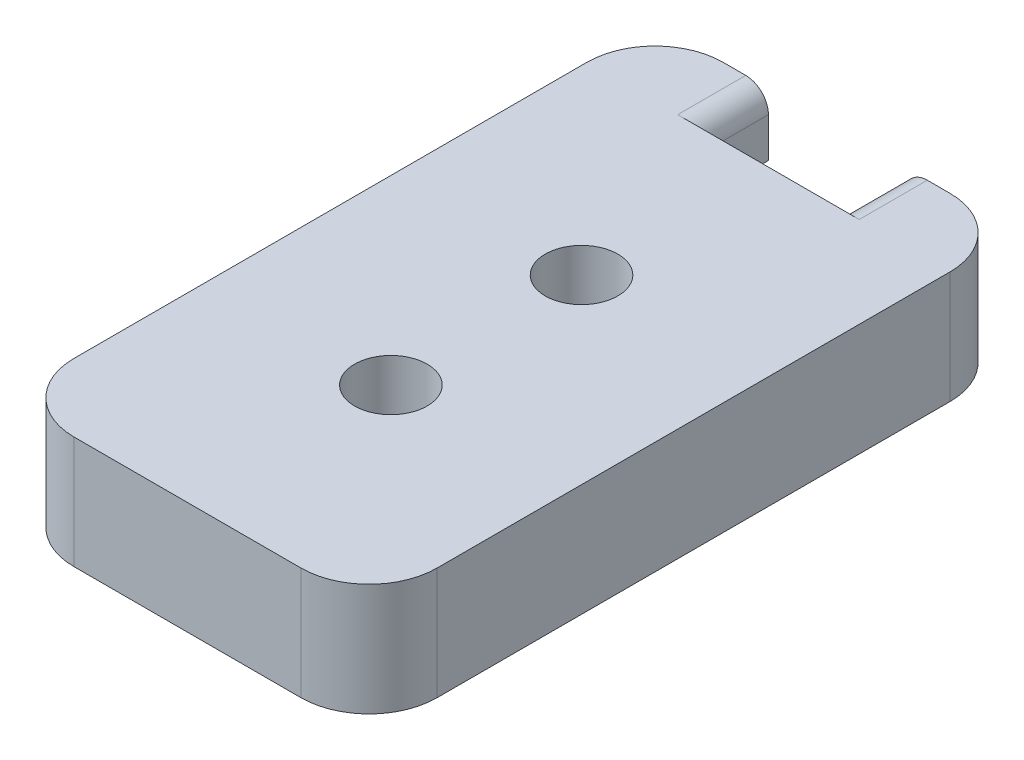
SolidWorks part; units mm, degrees
ref_plane "前视基准面" through (0, 0, 0) normal (0, 0, 1) x (1, 0, 0)
ref_plane "上视基准面" through (0, 0, 0) normal (0, 1, 0) x (1, 0, 0)
ref_plane "右视基准面" through (0, 0, 0) normal (1, 0, 0) x (0, 0, -1)
sketch "草图2" plane through (0, 0, 0) normal (0, 0, 1) x (1, 0, 0)
  line L0 (0, 0) -> (20, 0)
  line L1 (20, 0) -> (20, -4.95)
  line L2 (20, -4.95) -> (0, -4.95)
  line L3 (0, -4.95) -> (0, 0)
  point P2 (0, 0)
  point P5 (0, 0)
  point P6 (0, 0)
  point P7 (0, 0)
  point P8 (0, 0)
  point P9 (0.8017, 0)
extrude "凸台-拉伸1" add sketch "草图2" along normal blind 25.6
sketch "草图3" plane through (0, 0, 0) normal (0, 1, 0) x (1, 0, 0)
  circle A0 centre (10, -8.2367) radius 1.6
  circle A1 centre (10, -16.6367) radius 1.6
  dimension "D1" = 3.2
  dimension "D2" = 3.2
extrude "切除-拉伸1" cut sketch "草图3" against normal through all
sketch "草图4" plane through (0, 0, 0) normal (0, 0, -1) x (-1, 0, 0)
  line L0 (0, -4.95) -> (0, 0)
  line L1 (0, 0) -> (-20, 0)
  line L2 (-20, 0) -> (-20, -4.95)
  line L3 (-20, -4.95) -> (0, -4.95)
extrude "凸台-拉伸2" add sketch "草图4" along normal blind 3
sketch "草图5" plane through (0, 0, -3) normal (0, 0, -1) x (-1, 0, 0)
  line L0 (-10, 0) -> (-7, 0)
  line L1 (0, 0) -> (-20, 0) construction
  line L2 (-10, 0) -> (-13, 0)
  line L3 (-13, 0) -> (-13, -3)
  line L4 (-13, -3) -> (-7, -3)
  line L5 (-7, -3) -> (-7, 0)
extrude "切除-拉伸2" cut sketch "草图5" against normal blind 3
sketch "草图6" plane through (0, 0, -3) normal (0, 0, -1) x (-1, 0, 0)
  circle A1 centre (-7, -3) radius 0.25
  circle A2 centre (-13, -3) radius 0.25
  dimension "D1" = 0.5
  dimension "D2" = 0.5
extrude "切除-拉伸3" cut sketch "草图6" against normal blind 3
fillet "圆角2" radius 1 2 edges at (7, 0, -1.5) (13, 0, -1.5)
sketch "草图7" plane through (0, 0, -3) normal (0, 0, -1) x (-1, 0, 0)
  line L0 (0, 0) -> (-2, 0)
  line L3 (0, 0) -> (-6, 0) construction
  line L4 (-2, 0) -> (-2, -4.95)
  line L5 (-20, -4.95) -> (0, -4.95) construction
  line L6 (-2, -4.95) -> (0, -4.95)
  line L7 (0, -4.95) -> (0, 0)
  line L8 (-20, 0) -> (-18, 0)
  line L9 (-14, 0) -> (-20, 0) construction
  line L10 (-18, 0) -> (-18, -4.95)
  line L11 (-18, -4.95) -> (-20, -4.95)
  line L12 (-20, 0) -> (-20, -4.95) construction
  line L13 (-20, -4.95) -> (-20, 0)
extrude "切除-拉伸4" cut sketch "草图7" against normal through all
fillet "圆角3" radius 3 4 edges at (18, -2.475, 25.6) (2, -2.475, 25.6) (2, -2.475, -3) (18, -2.475, -3)
